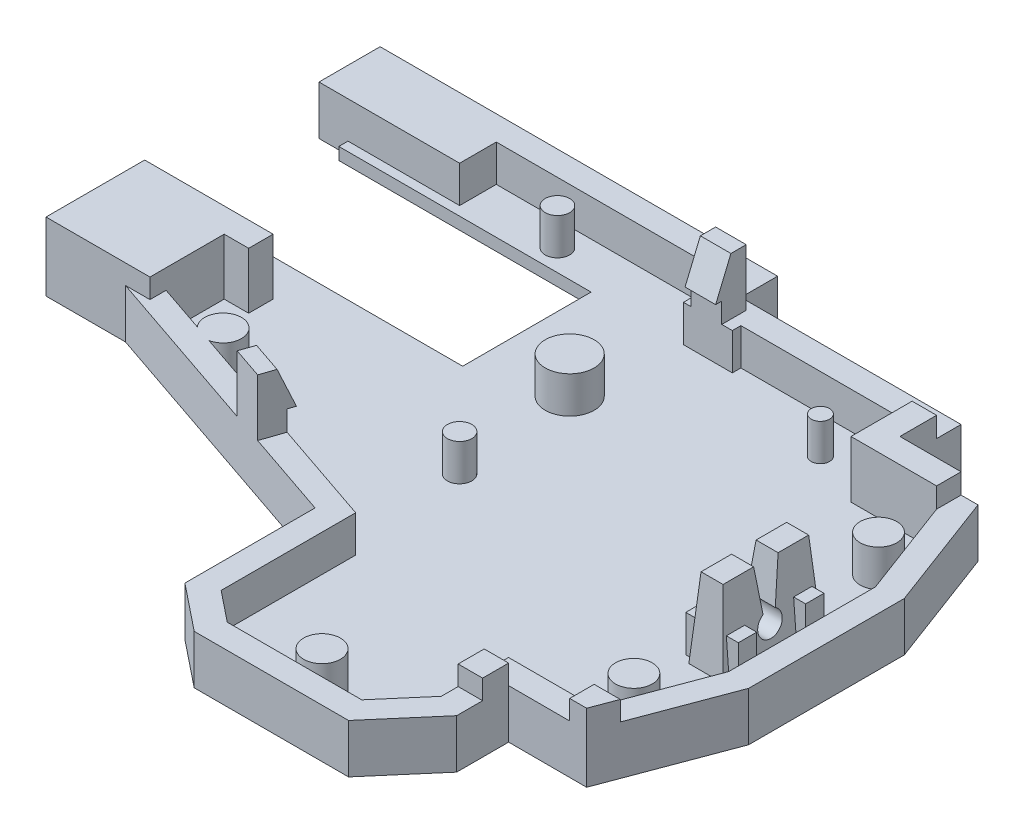
SolidWorks part; units mm, degrees
ref_plane "Front Plane" through (0, 0, 0) normal (0, 0, 1) x (1, 0, 0)
ref_plane "Top Plane" through (0, 0, 0) normal (0, 1, 0) x (1, 0, 0)
ref_plane "Right Plane" through (0, 0, 0) normal (1, 0, 0) x (0, 0, -1)
sketch "Sketch13" plane through (0, 0, 0) normal (0, 1, 0) x (1, 0, 0)
  line L1 (0, 0) -> (50, 0)
  line L2 (0, 0) -> (0, -45)
  line L3 (0, -45) -> (50, -45)
  line L4 (50, 0) -> (50, -45)
  dimension "D1" = 50
extrude "Boss-Extrude4" add sketch "Sketch13" along normal blind 1.6
sketch "Sketch14" plane through (0, 1.6, 0) normal (0, 1, 0) x (1, 0, 0)
  line L1 (50, 0) -> (40, 0)
  line L2 (50, 0) -> (50, -8)
  line L3 (50, -8) -> (40, -8)
  line L4 (40, 0) -> (40, -8)
extrude "Cut-Extrude6" cut sketch "Sketch14" against normal through all
sketch "Sketch15" plane through (0, 1.6, 0) normal (0, 1, 0) x (1, 0, 0)
  line L1 (40, 0) -> (22, 0)
  line L2 (40, 0) -> (40, -3)
  line L3 (40, -3) -> (22, -3)
  line L4 (22, 0) -> (22, -3)
extrude "Cut-Extrude7" cut sketch "Sketch15" against normal through all
sketch "Sketch16" plane through (0, 1.6, 0) normal (0, 1, 0) x (1, 0, 0)
  line L1 (22, -3) -> (26, -3)
  line L2 (22, -3) -> (22, -3.7)
  line L3 (22, -3.7) -> (26, -3.7)
  line L4 (26, -3) -> (26, -3.7)
  dimension "D1" = 0.7
  dimension "D2" = 4
extrude "Cut-Extrude8" cut sketch "Sketch16" against normal through all
sketch "Sketch17" plane through (0, 1.6, 0) normal (0, 1, 0) x (1, 0, 0)
  line L3 (40, -8) -> (50, -8) construction
  line L4 (47, -8) -> (50, -16)
  line L6 (50, -45) -> (50, -8) construction
  line L7 (50, -16) -> (65.8811, -16)
  line L8 (65.8811, -16) -> (65.8811, 17.9573)
  line L9 (65.8811, 17.9573) -> (47, 17.9573)
  line L10 (47, 17.9573) -> (47, -8)
extrude "Cut-Extrude9" cut sketch "Sketch17" against normal through all
sketch "Sketch18" plane through (0, 1.6, 0) normal (0, 1, 0) x (1, 0, 0)
  line L0 (40, -8) -> (40, -36) construction
  line L2 (40, -36) -> (61.1096, -36)
  line L3 (40, -36) -> (40, -58.8405)
  line L4 (40, -58.8405) -> (61.1096, -58.8405)
  line L5 (61.1096, -36) -> (61.1096, -58.8405)
extrude "Cut-Extrude10" cut sketch "Sketch18" against normal through all
sketch "Sketch21" plane through (0, 1.6, 0) normal (0, 1, 0) x (1, 0, 0)
  line L0 (50, -16) -> (27.9365, -16) construction
  line L1 (47, -36) -> (47, -28) construction
  line L2 (50, -36) -> (40, -36) construction
  line L3 (50, -28) -> (47, -36)
  line L4 (50, -36) -> (50, -16) construction
  line L5 (47, -36) -> (47, -49.2976)
  line L6 (47, -49.2976) -> (75.1968, -49.2976)
  line L7 (75.1968, -49.2976) -> (75.1968, -28)
  line L8 (75.1968, -28) -> (50, -28)
extrude "Cut-Extrude11" cut sketch "Sketch21" against normal through all
sketch "Sketch22" plane through (0, 1.6, 0) normal (0, 1, 0) x (1, 0, 0)
  line L0 (0, 0) -> (0, -19.3362) construction
  line L1 (0, 0) -> (0, -45) construction
  line L4 (0, -19.3362) -> (2, -19.3362)
  line L5 (0, -19.3362) -> (0, -22.3362)
  line L6 (0, -22.3362) -> (2, -22.3362)
  line L7 (2, -19.3362) -> (2, -22.3362)
  dimension "D1" = 2
  dimension "D2" = 3
extrude "Cut-Extrude12" cut sketch "Sketch22" against normal through all
sketch "Sketch23" plane through (0, 1.6, 0) normal (0, 1, 0) x (1, 0, 0)
  line L0 (40, -45) -> (23.5, -45) construction
  line L1 (0, -45) -> (40, -45) construction
  line L2 (23.5, -45) -> (23.5, -32)
  line L3 (0, -22.3362) -> (0, -26.3362) construction
  line L4 (0, -22.3362) -> (0, -45) construction
  line L5 (23.5, -32) -> (0, -26.3362)
  line L6 (0, -26.3362) -> (-30.2262, -26.3362)
  line L7 (-30.2262, -26.3362) -> (-30.2262, -63.1883)
  line L8 (-30.2262, -63.1883) -> (23.5, -63.1883)
  line L9 (23.5, -63.1883) -> (23.5, -45)
extrude "Cut-Extrude13" cut sketch "Sketch23" against normal through all
sketch "Sketch24" plane through (0, 1.6, 0) normal (0, 1, 0) x (1, 0, 0)
  line L0 (23.5, -43) -> (7.4911, -43)
  line L1 (23.5, -45) -> (40, -45) construction
  line L2 (7.4911, -43) -> (7.4911, -69.5502)
  line L3 (40, -36) -> (40, -45) construction
  line L4 (37, -45) -> (40, -41.5)
  line L5 (23.5, -45) -> (23.5, -32) construction
  line L6 (26, -45) -> (23.5, -43)
  line L7 (7.4911, -69.5502) -> (44.754, -69.5502)
  line L8 (44.754, -69.5502) -> (44.754, -41.5)
  line L9 (44.754, -41.5) -> (40, -41.5)
  line L10 (37, -45) -> (26, -45)
extrude "Cut-Extrude14" cut sketch "Sketch24" against normal through all
sketch "Sketch25" plane through (0, 1.6, 0) normal (0, 1, 0) x (1, 0, 0)
  line L0 (50, -22) -> (47.6007, -22.0598) construction
  line L1 (50, -28) -> (50, -16) construction
  line L2 (47.6007, -22.0598) -> (47.6007, -18.0598) construction
  line L4 (47.6007, -18.0598) -> (44.8007, -18.0598)
  line L5 (47.6007, -18.0598) -> (47.6007, -26.0598)
  line L6 (47.6007, -26.0598) -> (44.8007, -26.0598)
  line L7 (44.8007, -18.0598) -> (44.8007, -26.0598)
  dimension "D1" = 2.8
  dimension "D2" = 8
extrude "Cut-Extrude15" cut sketch "Sketch25" against normal through all
sketch "Sketch28" plane through (0, 0, 0) normal (0, -1, 0) x (1, 0, 0)
  line L44 (42, 38) -> (42, 42.2398)
  line L45 (42, 42.2398) -> (37.9199, 47)
  line L46 (37.9199, 47) -> (25.2984, 47)
  line L47 (25.2984, 47) -> (21.5, 43.9612)
  line L48 (21.5, 43.9612) -> (21.5, 33.5752)
  line L49 (21.5, 33.5752) -> (-2, 27.9115)
  line L50 (-2, 27.9115) -> (-2, -2)
  line L51 (-2, -2) -> (24, -2)
  line L52 (24, -2) -> (24, 1)
  line L53 (24, 1) -> (42, 1)
  line L54 (42, 1) -> (42, 6)
  line L55 (42, 6) -> (48.386, 6)
  line L56 (48.386, 6) -> (52, 15.6373)
  line L57 (52, 15.6373) -> (52, 28.3627)
  line L58 (52, 28.3627) -> (48.386, 38)
  line L59 (48.386, 38) -> (42, 38)
  line L60 (42, 38) -> (42, 42.2398)
  line L61 (42, 42.2398) -> (37.9199, 47)
  line L62 (37.9199, 47) -> (25.2984, 47)
  line L63 (25.2984, 47) -> (21.5, 43.9612)
  line L64 (21.5, 43.9612) -> (21.5, 33.5752)
  line L65 (21.5, 33.5752) -> (-2, 27.9115)
  line L66 (-2, 27.9115) -> (-2, -2)
  line L67 (-2, -2) -> (24, -2)
  line L68 (24, -2) -> (24, 1)
  line L69 (24, 1) -> (42, 1)
  line L70 (42, 1) -> (42, 6)
  line L71 (42, 6) -> (48.386, 6)
  line L72 (48.386, 6) -> (52, 15.6373)
  line L73 (52, 15.6373) -> (52, 28.3627)
  line L74 (52, 28.3627) -> (48.386, 38)
  line L75 (48.386, 38) -> (42, 38)
  dimension "D1" = 2
extrude "Boss-Extrude6" add sketch "Sketch28" along normal blind 6
sketch "Sketch30" plane through (0, 0, 0) normal (0, 1, 0) x (1, 0, 0)
  line L8 (44.8007, -18.0598) -> (44.8007, -26.0598)
  line L9 (44.8007, -26.0598) -> (47.6007, -26.0598)
  line L10 (47.6007, -26.0598) -> (47.6007, -18.0598)
  line L11 (47.6007, -18.0598) -> (44.8007, -18.0598)
  line L12 (44.8007, -18.0598) -> (44.8007, -26.0598)
  line L13 (44.8007, -26.0598) -> (47.6007, -26.0598)
  line L14 (47.6007, -26.0598) -> (47.6007, -18.0598)
  line L15 (47.6007, -18.0598) -> (44.8007, -18.0598)
  dimension "D1" = 0
extrude "Boss-Extrude7" add sketch "Sketch30" along normal blind 3.5
sketch "Sketch31" plane through (0, 1.6, 0) normal (0, 1, 0) x (1, 0, 0)
  line L44 (37, -45) -> (40, -41.5)
  line L45 (40, -41.5) -> (40, -36)
  line L46 (40, -36) -> (47, -36)
  line L47 (47, -36) -> (50, -28)
  line L48 (50, -28) -> (50, -16)
  line L49 (50, -16) -> (47, -8)
  line L50 (47, -8) -> (40, -8)
  line L51 (40, -8) -> (40, -3)
  line L52 (40, -3) -> (26, -3)
  line L53 (26, -3) -> (26, -3.7)
  line L54 (26, -3.7) -> (22, -3.7)
  line L55 (22, -3.7) -> (22, 0)
  line L56 (22, 0) -> (0, 0)
  line L57 (0, 0) -> (0, -19.3362)
  line L58 (0, -19.3362) -> (2, -19.3362)
  line L59 (2, -19.3362) -> (2, -22.3362)
  line L60 (2, -22.3362) -> (0, -22.3362)
  line L61 (0, -22.3362) -> (0, -26.3362)
  line L62 (0, -26.3362) -> (23.5, -32)
  line L63 (23.5, -32) -> (23.5, -43)
  line L64 (23.5, -43) -> (26, -45)
  line L65 (26, -45) -> (37, -45)
  line L66 (37, -45) -> (40, -41.5)
  line L67 (40, -41.5) -> (40, -36)
  line L68 (40, -36) -> (47, -36)
  line L69 (47, -36) -> (50, -28)
  line L70 (50, -28) -> (50, -16)
  line L71 (50, -16) -> (47, -8)
  line L72 (47, -8) -> (40, -8)
  line L73 (40, -8) -> (40, -3)
  line L74 (40, -3) -> (26, -3)
  line L75 (26, -3) -> (26, -3.7)
  line L76 (26, -3.7) -> (22, -3.7)
  line L77 (22, -3.7) -> (22, 0)
  line L78 (22, 0) -> (0, 0)
  line L79 (0, 0) -> (0, -19.3362)
  line L80 (0, -19.3362) -> (2, -19.3362)
  line L81 (2, -19.3362) -> (2, -22.3362)
  line L82 (2, -22.3362) -> (0, -22.3362)
  line L83 (0, -22.3362) -> (0, -26.3362)
  line L84 (0, -26.3362) -> (23.5, -32)
  line L85 (23.5, -32) -> (23.5, -43)
  line L86 (23.5, -43) -> (26, -45)
  line L87 (26, -45) -> (37, -45)
  dimension "D1" = 0
extrude "Cut-Extrude16" cut sketch "Sketch31" against normal blind 4.6
sketch "Sketch32" plane through (0, 1.6, 0) normal (0, -1, 0) x (1, 0, 0)
  line L8 (47.6007, 18.0598) -> (47.6007, 26.0598)
  line L9 (47.6007, 26.0598) -> (44.8007, 26.0598)
  line L10 (44.8007, 26.0598) -> (44.8007, 18.0598)
  line L11 (44.8007, 18.0598) -> (47.6007, 18.0598)
  line L12 (47.6007, 18.0598) -> (47.6007, 26.0598)
  line L13 (47.6007, 26.0598) -> (44.8007, 26.0598)
  line L14 (44.8007, 26.0598) -> (44.8007, 18.0598)
  line L15 (44.8007, 18.0598) -> (47.6007, 18.0598)
  dimension "D1" = 0
extrude "Boss-Extrude8" add sketch "Sketch32" along normal blind 4.6
sketch "Sketch35" plane through (47.6007, 0, 0) normal (1, 0, 0) x (0, 0, -1)
  line L0 (-22.0598, 3.5) -> (-22.0598, 0) construction
  line L1 (-26.0598, 3.5) -> (-18.0598, 3.5) construction
  line L2 (-22.0598, 3.5) -> (-21.0598, 3.5) construction
  line L3 (-22.0598, 3.5) -> (-23.0598, 3.5) construction
  line L4 (-22.0598, 0) -> (-21.5598, 0)
  line L5 (-21.5598, 0) -> (-21.0598, 3.5)
  line L6 (-22.0598, 0) -> (-22.5598, 0)
  line L7 (-22.5598, 0) -> (-23.0598, 3.5)
  line L8 (-23.0598, 3.5) -> (-23.2577, 4.8851)
  line L9 (-21.0598, 3.5) -> (-21.2977, 5.1651)
  line L10 (-21.2977, 5.1651) -> (-23.2577, 4.8851)
extrude "Cut-Extrude18" cut sketch "Sketch35" against normal blind 4.6
sketch "Sketch37" plane through (47.6007, 0, 0) normal (1, 0, 0) x (0, 0, -1)
  line L0 (-22.0598, 0) -> (-22.0598, -3.4808) construction
  line L1 (-22.5598, 0) -> (-21.5598, 0) construction
  line L2 (-21.5598, 0) -> (-22.0598, -0.866) construction
  circle A0 centre (-22.0598, -0.866) radius 1
extrude "Cut-Extrude19" cut sketch "Sketch37" against normal blind 4.6
sketch "Sketch39" plane through (44.8007, 0, 0) normal (-1, 0, 0) x (0, 0, 1)
  line L0 (26.0598, 3.5) -> (25.5598, 3.5) construction
  line L1 (23.0598, 3.5) -> (26.0598, 3.5) construction
  line L2 (25.5598, 3.5) -> (26.0598, -3)
  line L3 (26.0598, -3) -> (27.9064, -2.858)
  line L4 (27.9064, -2.858) -> (27.4064, 3.642)
  line L5 (27.4064, 3.642) -> (25.5598, 3.5)
  line L6 (18.0598, 3.5) -> (18.5598, 3.5) construction
  line L7 (18.0598, 3.5) -> (21.0598, 3.5) construction
  line L8 (18.5598, 3.5) -> (18.0598, -3)
  line L9 (18.0598, -3) -> (15.9573, -2.8383)
  line L10 (15.9573, -2.8383) -> (16.4557, 3.642)
  line L11 (16.4557, 3.642) -> (18.5598, 3.5)
extrude "Cut-Extrude20" cut sketch "Sketch39" against normal blind 4.6
sketch "Sketch41" plane through (0, 0, 0) normal (0, 0, 1) x (1, 0, 0)
  line L0 (44.8007, 3.5) -> (45.3007, 3.5) construction
  line L1 (44.8007, 3.5) -> (47.6007, 3.5) construction
  line L2 (47.6007, 3.5) -> (47.1007, 3.5) construction
  line L3 (45.3007, 3.5) -> (44.8007, -3)
  line L4 (44.8007, -3) -> (43.415, -2.8934)
  line L5 (43.415, -2.8934) -> (43.9406, 3.9398)
  line L6 (43.9406, 3.9398) -> (45.3007, 3.5)
  line L7 (47.1007, 3.5) -> (47.6007, -3)
  line L8 (47.6007, -3) -> (49.659, -2.8417)
  line L9 (49.659, -2.8417) -> (49.1373, 3.9398)
  line L10 (49.1373, 3.9398) -> (47.1007, 3.5)
extrude "Cut-Extrude21" cut sketch "Sketch41" along normal up to vertex
sketch "Sketch43" plane through (0, 0, 0) normal (0, 1, 0) x (1, 0, 0)
  line L0 (47, -8) -> (50, -16)
  line L1 (50, -16) -> (51.1704, -13.4251)
  line L2 (49.4404, -8.8117) -> (52, -15.6373) construction
  line L3 (46.2007, -6) -> (51.8278, -6) construction
  line L4 (45.0315, -6) -> (47.37, -6) construction
  line L5 (50.6159, -11.9464) -> (47.8466, -4.5615) construction
  line L6 (51.1704, -13.4251) -> (48.386, -6)
  line L7 (48.386, -6) -> (42.8188, -6)
  line L8 (42, -6) -> (43.6375, -6) construction
  line L9 (42.8188, -6) -> (42.8188, -8)
  line L10 (40, -8) -> (43.6375, -8) construction
  line L11 (42.8188, -8) -> (47, -8)
extrude "Boss-Extrude9" add sketch "Sketch43" against normal blind 4.6
sketch "Sketch44" plane through (0, -3, 0) normal (0, 1, 0) x (1, 0, 0)
  line L0 (47.6007, -18.0598) -> (47.6007, -18.5598) construction
  line L1 (47.6007, -18.0598) -> (47.6007, -26.0598) construction
  line L2 (47.6007, -18.5598) -> (48.3507, -18.5598) construction
  line L3 (44.8007, -18.5598) -> (44.0507, -18.5598) construction
  line L4 (44.8007, -26.0598) -> (44.8007, -18.0598) construction
  line L5 (47.6007, -26.0598) -> (47.6007, -25.5598) construction
  line L6 (48.3507, -25.5598) -> (44.0507, -25.5598) construction
  line L7 (48.3507, -18.5598) -> (48.3507, -20.0598)
  line L8 (48.3507, -25.5598) -> (48.3507, -24.0598)
  line L9 (48.3507, -24.0598) -> (44.0507, -24.0598)
  line L10 (44.0507, -24.0598) -> (44.0507, -25.5598)
  line L11 (44.0507, -25.5598) -> (48.3507, -25.5598)
  line L12 (48.3507, -20.0598) -> (44.0507, -20.0598)
  line L13 (44.0507, -20.0598) -> (44.0507, -18.5598)
  line L14 (44.0507, -18.5598) -> (48.3507, -18.5598)
extrude "Boss-Extrude11" add sketch "Sketch44" along normal blind 3
sketch "Sketch45" plane through (0, -3, 0) normal (0, 1, 0) x (1, 0, 0)
  line L0 (50, -22) -> (44, -22) construction
  line L1 (50, -28) -> (50, -16) construction
  line L2 (44, -22) -> (44, -32) construction
  line L3 (44, -32) -> (46.25, -32) construction
  line L4 (44, -22) -> (44, -12) construction
  line L5 (22, -3.7) -> (22, -22) construction
  line L6 (22, -22) -> (22, -21) construction
  line L7 (40, -36) -> (23.5, -36) construction
  line L8 (23.5, -32) -> (23.5, -43) construction
  line L9 (31.75, -45) -> (31.75, -43) construction
  line L10 (26, -45) -> (37, -45) construction
  line L11 (40, -3) -> (40, -6) construction
  line L12 (40, -8) -> (40, -3) construction
  line L13 (40, -6) -> (35.5, -6) construction
  line L14 (22, 0) -> (22, -2) construction
  line L15 (22, 0) -> (0, 0) construction
  line L16 (22, -3.7) -> (22, 0) construction
  line L17 (22, -2) -> (10, -2) construction
  line L18 (0, -24.3362) -> (5, -24.3362) construction
  line L19 (0, -22.3362) -> (0, -26.3362) construction
  circle A0 centre (46.25, -12) radius 1.5
  circle A1 centre (46.25, -32) radius 1.5
  circle A2 centre (22, -22) radius 1
  circle A3 centre (21, -12) radius 1.9996
  circle A4 centre (31.75, -43) radius 1.5033
  circle A5 centre (35.5, -6) radius 0.75
  circle A6 centre (10, -2) radius 1
  circle A7 centre (5, -24.3362) radius 1.5
extrude "Boss-Extrude12" add sketch "Sketch45" along normal blind 3
sketch "Sketch46" plane through (0, 0, 0) normal (0, 1, 0) x (1, 0, 0)
  line L0 (14.1373, -29.7435) -> (16.5677, -30.3292)
  line L1 (16.5677, -30.3292) -> (16.0991, -32.2736)
  line L2 (21.5, -33.5752) -> (-2, -27.9115) construction
  line L3 (16.0991, -32.2736) -> (13.6687, -31.6878)
  line L4 (13.6687, -31.6878) -> (14.1373, -29.7435)
  line L5 (24, -3.7) -> (25.1336, -3.7) construction
  line L6 (22, -3.7) -> (26, -3.7) construction
  line L7 (25.1336, -3.7) -> (22.6336, -3.7)
  line L8 (22.6336, -3.7) -> (22.6336, -1.7)
  line L9 (22.6336, -1.7) -> (25.1336, -1.7)
  line L10 (25.1336, -1.7) -> (25.1336, -3.7)
  line L11 (2, -20.8362) -> (2, -19.9327) construction
  line L12 (2, -22.3362) -> (2, -19.3362) construction
  line L13 (2, -19.9327) -> (2, -21.9327)
  line L14 (2, -21.9327) -> (0, -21.9327)
  line L15 (0, -21.9327) -> (0, -19.9327)
  line L16 (0, -19.9327) -> (2, -19.9327)
  line L17 (23.5, -32) -> (0, -26.3362) construction
  line L18 (16.5677, -30.3292) -> (14.1373, -29.7435) construction
  line L19 (47, -36) -> (48.8727, -36.7022)
  line L20 (52, -28.3627) -> (48.386, -38) construction
  line L21 (48.8727, -36.7022) -> (49.7505, -34.3614)
  line L22 (49.7505, -34.3614) -> (47.8778, -33.6592)
  line L23 (50, -28) -> (47, -36) construction
  line L24 (47.8778, -33.6592) -> (47, -36)
  line L25 (40, -3) -> (40, -8)
  line L26 (26, -3) -> (40, -3) construction
  line L27 (40, -3) -> (40, -8) construction
  line L28 (40, -8) -> (47, -8)
  line L29 (47, -8) -> (47, -6)
  line L30 (42, -6) -> (48.386, -6) construction
  line L31 (47, -6) -> (42, -6)
  line L32 (42, -6) -> (42, -3)
  line L33 (42, -1) -> (42, -6) construction
  line L34 (42, -3) -> (40, -3)
extrude "Boss-Extrude13" add sketch "Sketch46" along normal blind 1.65
sketch "Sketch47" plane through (0, 0, 0) normal (0, 1, 0) x (1, 0, 0)
  line L1 (0, 0) -> (3, 0)
  line L2 (0, 0) -> (0, -3)
  line L3 (0, -3) -> (3, -3)
  line L4 (3, 0) -> (3, -3)
extrude "Boss-Extrude14" add sketch "Sketch47" against normal up to surface (3 mm away) up to face at (10, -3, 3)
sketch "Sketch48" plane through (0, 0, 0) normal (0, 1, 0) x (1, 0, 0)
  line L0 (-2, -27.9115) -> (-2, 2) construction
  line L1 (0, -19.3362) -> (-2, -19.3362)
  line L2 (0, -19.3362) -> (0, -3)
  line L3 (0, -3) -> (-2, -3)
  line L4 (-2, -19.3362) -> (-2, -3)
extrude "Cut-Extrude22" cut sketch "Sketch48" against normal up to surface (3 mm away) up to face at (23.75, -3, 19.4826)
sketch "Sketch49" plane through (-2, 0, 0) normal (-1, 0, 0) x (0, 0, 1)
  line L1 (-2, -6) -> (19.3362, -6)
  line L2 (-2, -6) -> (-2, -3)
  line L3 (-2, -3) -> (19.3362, -3)
  line L4 (19.3362, -6) -> (19.3362, -3)
extrude "Boss-Extrude15" add sketch "Sketch49" along normal blind 13
sketch "Sketch50" plane through (0, -6, 0) normal (0, -1, 0) x (1, 0, 0)
  line L0 (52, 22) -> (52, -11.4177) construction
  line L1 (52, 15.6373) -> (52, 28.3627) construction
  line L2 (24, -2) -> (52, -2) construction
  line L3 (52, 22) -> (52, 58.8348) construction
  line L4 (34.4271, 47) -> (52, 47) construction
  line L5 (37.9199, 47) -> (25.2984, 47) construction
  line L7 (-15, -2) -> (52, -2)
  line L8 (-15, -2) -> (-15, 47)
  line L9 (-15, 47) -> (52, 47)
  line L10 (52, -2) -> (52, 47)
extrude "Boss-Extrude16" add sketch "Sketch50" against normal up to surface (3 mm away) up to face at (19.6296, -3, 17.9784)
sketch "Sketch51" plane through (0, -3, 0) normal (0, 1, 0) x (1, 0, 0)
  line L0 (47.6007, -26.0598) -> (47.6007, -47) construction
  line L1 (52, -47) -> (37.9199, -47) construction
  line L3 (47, -36) -> (52, -36)
  line L4 (47, -36) -> (47, -47)
  line L5 (47, -47) -> (52, -47)
  line L6 (52, -36) -> (52, -47)
extrude "Boss-Extrude17" add sketch "Sketch51" along normal blind 15.6
sketch "Sketch52" plane through (0, 1.65, 0) normal (0, 1, 0) x (1, 0, 0)
  line L8 (47.8778, -33.6592) -> (47, -36)
  line L9 (47, -36) -> (49.136, -36)
  line L10 (49.136, -36) -> (49.7505, -34.3614)
  line L11 (49.7505, -34.3614) -> (47.8778, -33.6592)
  line L12 (47.8778, -33.6592) -> (47, -36)
  line L13 (47, -36) -> (49.136, -36)
  line L14 (49.136, -36) -> (49.7505, -34.3614)
  line L15 (49.7505, -34.3614) -> (47.8778, -33.6592)
  dimension "D1" = 0
extrude "Cut-Extrude23" cut sketch "Sketch52" against normal up to surface (1.65 mm away) up to face at (49.3349, 0, 19.5578)
sketch "Sketch53" plane through (0, 0, 0) normal (0, 1, 0) x (1, 0, 0)
  line L0 (40, -36) -> (40, -41.5) construction
  line L1 (40, -37.9906) -> (42, -37.9906)
  line L2 (40, -37.9906) -> (40, -40.1199)
  line L3 (40, -40.1199) -> (42, -40.1199)
  line L4 (42, -37.9906) -> (42, -40.1199)
  line L5 (42, -38) -> (42, -42.2398) construction
extrude "Boss-Extrude18" add sketch "Sketch53" along normal blind 1.6
sketch "Sketch55" plane through (0, 1.65, 0) normal (0, 1, 0) x (1, 0, 0)
  line L1 (22.6336, -1.7) -> (25.1336, -1.7)
  line L2 (22.6336, -1.7) -> (22.6336, -4.2)
  line L3 (22.6336, -4.2) -> (25.1336, -4.2)
  line L4 (25.1336, -1.7) -> (25.1336, -4.2)
extrude "Boss-Extrude20" add sketch "Sketch55" along normal blind 3
sketch "Sketch56" plane through (25.1336, 0, 0) normal (1, 0, 0) x (0, 0, -1)
  line L0 (-4.2, 1.65) -> (-2.95, 4.65)
  line L1 (-4.2, 4.65) -> (-1.7, 4.65) construction
  line L2 (-2.95, 4.65) -> (-2.95, 7.6873)
  line L3 (-2.95, 7.6873) -> (-6.5972, 7.6873)
  line L4 (-6.5972, 7.6873) -> (-6.5972, 1.6413)
  line L5 (-6.5972, 1.6413) -> (-4.2, 1.65)
extrude "Cut-Extrude24" cut sketch "Sketch56" against normal blind 3
sketch "Sketch58" plane through (0, -3, 0) normal (0, 1, 0) x (1, 0, 0)
  line L0 (3, 0) -> (-15, 0) construction
  line L1 (-15, -47) -> (-15, 2) construction
  line L2 (0, -26.3362) -> (7.3396, -26.3362) construction
  line L3 (-15, -19.3362) -> (-15, -16.4918) construction
  line L4 (3, 0) -> (3, -3.75) construction
  line L5 (3, -3.75) -> (-5.5, -3.75) construction
  line L6 (-5.5, -3.75) -> (14.5, -3.75)
  line L7 (-5.5, -3.75) -> (-5.5, -14.25)
  line L8 (-5.5, -14.25) -> (14.5, -14.25)
  line L9 (14.5, -3.75) -> (14.5, -14.25)
  line L10 (7.3396, 0) -> (7.3396, -26.3362) construction
  line L11 (22, 0) -> (3, 0) construction
  line L12 (26, -45) -> (6.087, -45) construction
  line L13 (6.087, 0) -> (6.087, -45) construction
  line L14 (0, 0) -> (0, -25) construction
  line L15 (0, -22.3362) -> (0, -26.3362) construction
  line L16 (0, -14.25) -> (0, -17.2489) construction
  line L17 (2, -20.8362) -> (2, -17.2489) construction
  line L18 (2, -19.3362) -> (2, -22.3362) construction
  line L19 (0, -17.2489) -> (2, -17.2489)
  line L20 (2, -17.2489) -> (2, -19.2489)
  line L21 (2, -19.2489) -> (0, -19.2489)
  line L22 (0, -19.2489) -> (0, -17.2489)
extrude "Cut-Extrude29" cut sketch "Sketch58" against normal blind 1
sketch "Sketch60" plane through (0, -3, 0) normal (0, 1, 0) x (1, 0, 0)
  line L0 (27.9182, -45) -> (13.2629, -45) construction
  line L1 (26, -45) -> (37, -45) construction
  line L2 (23.5, -32) -> (23.5, -45) construction
  line L3 (0, 0) -> (0, -24) construction
  line L4 (0, -22.3362) -> (0, -26.3362) construction
  line L5 (0, -24) -> (23.5, -32)
  line L6 (23.5, -32) -> (0, -26.3362)
  line L7 (0, -26.3362) -> (23.5, -32) construction
  line L8 (0, -26.3362) -> (0, -24)
extrude "Boss-Extrude21" add sketch "Sketch60" along normal up to surface (3 mm away) up to face at (49.1691, 0, 20)
sketch "Sketch61" plane through (-5.9989, 0, 24.8904) normal (0.2343, 0, -0.9722) x (-0.9722, 0, -0.2343)
  line L8 (-23.2128, 1.65) -> (-23.2128, 0)
  line L9 (-23.2128, 0) -> (-20.7128, 0)
  line L10 (-20.7128, 0) -> (-20.7128, 1.65)
  line L11 (-20.7128, 1.65) -> (-23.2128, 1.65)
  line L12 (-23.2128, 1.65) -> (-23.2128, 0)
  line L13 (-23.2128, 0) -> (-20.7128, 0)
  line L14 (-20.7128, 0) -> (-20.7128, 1.65)
  line L15 (-20.7128, 1.65) -> (-23.2128, 1.65)
  dimension "D1" = 0
extrude "Boss-Extrude22" add sketch "Sketch61" along normal up to surface (0.8848 mm away)
sketch "Sketch62" plane through (0, 0, 0) normal (0, 1, 0) x (1, 0, 0)
  line L0 (0, -24) -> (0, -26) construction
  line L1 (1.9318, -24.6576) -> (-9.2599, -20.8477) construction
  line L2 (3.8635, -25.3152) -> (0, -24) construction
  line L3 (-9.2599, -20.8477) -> (-9.2599, -22.8477) construction
  line L4 (0, -26) -> (-0.5452, -28.2621)
  line L5 (13.6687, -31.6878) -> (-2, -27.9115) construction
  line L6 (-0.5452, -28.2621) -> (-9.9311, -26)
  line L7 (-9.9311, -26) -> (-9.2599, -22.8477)
  line L8 (-9.2599, -22.8477) -> (0, -26)
extrude "Cut-Extrude30" cut sketch "Sketch62" against normal up to surface (3 mm away) up to face at (35.5, -3, 6.75)
sketch "Sketch63" plane through (-6.4675, 0, 26.8348) normal (-0.2343, 0, 0.9722) x (0.9722, 0, 0.2343)
  line L16 (20.7128, 0) -> (6.0919, 0)
  line L17 (6.0919, 0) -> (6.0919, -3)
  line L18 (6.0919, -3) -> (28.7683, -3)
  line L19 (28.7683, -3) -> (28.7683, 0)
  line L20 (28.7683, 0) -> (23.2128, 0)
  line L21 (23.2128, 0) -> (23.2128, 1.65)
  line L22 (23.2128, 1.65) -> (20.7128, 1.65)
  line L23 (20.7128, 1.65) -> (20.7128, 0)
  line L24 (20.7128, 0) -> (6.0919, 0)
  line L25 (6.0919, 0) -> (6.0919, -3)
  line L26 (6.0919, -3) -> (28.7683, -3)
  line L27 (28.7683, -3) -> (28.7683, 0)
  line L28 (28.7683, 0) -> (23.2128, 0)
  line L29 (23.2128, 0) -> (23.2128, 1.65)
  line L30 (23.2128, 1.65) -> (20.7128, 1.65)
  line L31 (20.7128, 1.65) -> (20.7128, 0)
  dimension "D1" = 0
extrude "Cut-Extrude31" cut sketch "Sketch63" against normal up to surface (0.7539 mm away)
sketch "Sketch64" plane through (0, 1.65, 0) normal (0, 1, 0) x (1, 0, 0)
  line L0 (0, -21.9327) -> (0, -22.9624) construction
  line L2 (0, -22.9624) -> (2.5515, -22.9624)
  line L3 (0, -22.9624) -> (0, -18.6516)
  line L4 (0, -18.6516) -> (2.5515, -18.6516)
  line L5 (2.5515, -22.9624) -> (2.5515, -18.6516)
extrude "Cut-Extrude32" cut sketch "Sketch64" against normal up to surface (4.65 mm away) up to face at (18.4683, -3, 21.8358)
sketch "Sketch65" plane through (0, -4, 0) normal (0, 1, 0) x (1, 0, 0)
  line L8 (0, -17.2489) -> (0, -19.2489)
  line L9 (0, -19.2489) -> (2, -19.2489)
  line L10 (2, -19.2489) -> (2, -17.2489)
  line L11 (2, -17.2489) -> (0, -17.2489)
  line L12 (0, -17.2489) -> (0, -19.2489)
  line L13 (0, -19.2489) -> (2, -19.2489)
  line L14 (2, -19.2489) -> (2, -17.2489)
  line L15 (2, -17.2489) -> (0, -17.2489)
  dimension "D1" = 0
extrude "Boss-Extrude23" add sketch "Sketch65" along normal up to surface (4 mm away) up to face at (49.1691, 0, 20)
sketch "Sketch66" plane through (0, 0, 0) normal (0, 1, 0) x (1, 0, 0)
  line L1 (0, -19.2489) -> (2, -19.2489)
  line L2 (0, -19.2489) -> (0, -17.2489)
  line L3 (0, -17.2489) -> (2, -17.2489)
  line L4 (2, -19.2489) -> (2, -17.2489)
extrude "Boss-Extrude24" add sketch "Sketch66" along normal blind 1.6
sketch "Sketch67" plane through (0, 1.6, 0) normal (0, 1, 0) x (1, 0, 0)
  line L0 (0, -19.2489) -> (2.5, -19.2489)
  line L1 (0, -19.2489) -> (0, -17.2489)
  line L2 (0, -17.2489) -> (2.5, -17.2489)
  line L3 (2.5, -17.2489) -> (2.5, -19.2489)
extrude "Boss-Extrude25" add sketch "Sketch67" along normal blind 3
sketch "Sketch68" plane through (0, 0, 17.2489) normal (0, 0, -1) x (-1, 0, 0)
  line L0 (-2.5, 1.6) -> (-1.25, 4.6)
  line L1 (-2.5, 4.6) -> (0, 4.6) construction
  line L2 (-1.25, 4.6) -> (-1.25, 6.7749)
  line L3 (-1.25, 6.7749) -> (-4.4975, 6.7749)
  line L4 (-4.4975, 6.7749) -> (-4.4975, 1.5671)
  line L5 (-4.4975, 1.5671) -> (-2.5, 1.6)
extrude "Cut-Extrude33" cut sketch "Sketch68" against normal blind 3
sketch "Sketch69" plane through (0, 1.65, 0) normal (0, 1, 0) x (1, 0, 0)
  line L0 (14.3446, -28.8833) -> (16.7212, -29.6923) construction
  line L1 (16.7212, -29.6923) -> (18.8289, -30.4098) construction
  line L2 (16.2758, -31.5407) -> (16.8859, -29.7484) construction
  line L3 (16.2758, -31.5407) -> (16.7212, -29.6923) construction
  line L4 (16.2758, -31.5407) -> (13.8992, -30.7316) construction
  line L5 (14.3446, -28.8833) -> (16.8859, -29.7484)
  line L6 (16.8859, -29.7484) -> (16.2758, -31.5407)
  line L7 (16.2758, -31.5407) -> (12.9279, -30.401) construction
  line L8 (14.3446, -28.8833) -> (13.7345, -30.6756)
  line L9 (13.7345, -30.6756) -> (16.2758, -31.5407)
extrude "Boss-Extrude26" add sketch "Sketch69" against normal up to surface (1.65 mm away) up to face at (49.1691, 0, 20)
sketch "Sketch70" plane through (0, 0, 19.2489) normal (0, 0, 1) x (1, 0, 0)
  line L0 (2.5, 1.6) -> (1.25, 4.6) construction
  line L1 (2.5, 1.6) -> (-2.555, 1.6)
  line L2 (2.5, 1.6) -> (2.5, 7.1604)
  line L3 (2.5, 7.1604) -> (-2.555, 7.1604)
  line L4 (-2.555, 1.6) -> (-2.555, 7.1604)
extrude "Cut-Extrude34" cut sketch "Sketch70" against normal blind 3
sketch "Sketch71" plane through (0, 1.65, 0) normal (0, 1, 0) x (1, 0, 0)
  line L0 (16.2758, -31.5407) -> (17.0814, -29.1741)
  line L1 (16.2758, -31.5407) -> (13.7345, -30.6756)
  line L2 (18.2187, -25.945) -> (17.0814, -29.1741) construction
  line L3 (18.2187, -25.945) -> (16.2758, -31.5407) construction
  line L4 (17.0814, -29.1741) -> (11.4228, -27.2093) construction
  line L5 (13.7345, -30.6756) -> (14.5598, -28.2985)
  line L6 (14.5598, -28.2985) -> (17.0814, -29.1741)
extrude "Boss-Extrude27" add sketch "Sketch71" along normal blind 3
sketch "Sketch72" plane through (24.2076, 0, 8.2409) normal (0.9466, 0, 0.3223) x (0.3223, 0, -0.9466)
  line L0 (-22.1129, 1.65) -> (-23.3629, 4.65)
  line L1 (-24.6129, 4.65) -> (-22.1129, 4.65) construction
  line L2 (-23.3629, 4.65) -> (-23.3629, 7.6948)
  line L3 (-23.3629, 7.6948) -> (-20.7348, 7.6948)
  line L4 (-20.7348, 7.6948) -> (-20.7348, 1.65)
  line L5 (-20.7348, 1.65) -> (-22.1129, 1.65)
extrude "Cut-Extrude35" cut sketch "Sketch72" against normal blind 3
sketch "Sketch73" plane through (21.762, 0, 7.5561) normal (-0.9447, 0, -0.328) x (-0.328, 0, 0.9447)
  line L10 (24.4734, 4.65) -> (23.2234, 4.65)
  line L11 (23.2234, 4.65) -> (21.9734, 1.65)
  line L12 (21.9734, 1.65) -> (22.5801, 1.65)
  line L13 (22.5801, 1.65) -> (24.4734, 1.65)
  line L14 (24.4734, 1.65) -> (24.4734, 4.65)
  line L15 (24.4734, 4.65) -> (23.2234, 4.65)
  line L16 (23.2234, 4.65) -> (21.9734, 1.65)
  line L17 (21.9734, 1.65) -> (22.5801, 1.65)
  line L18 (22.5801, 1.65) -> (24.4734, 1.65)
  line L19 (24.4734, 1.65) -> (24.4734, 4.65)
  dimension "D1" = 0
extrude "Boss-Extrude28" add sketch "Sketch73" along normal up to surface (0.0115 mm away)
sketch "Sketch74" plane through (0, -4, 0) normal (0, 1, 0) x (1, 0, 0)
  line L0 (-5.5, -9) -> (14.5, -9) construction
  line L1 (-5.5, -3.75) -> (-5.5, -14.25) construction
  line L2 (14.5, -14.25) -> (14.5, -3.75) construction
  line L3 (-0.25, -6.1692) -> (-0.25, -11.6692) construction
  line L4 (4.5, -6.1692) -> (4.5, -11.6692) construction
  line L5 (-0.25, -6.1692) -> (9.25, -6.1692) construction
  line L6 (9.25, -6.1692) -> (9.25, -11.6692) construction
  line L7 (2.5808, -9) -> (-0.25, -6.1692) construction
  line L8 (6.4192, -6.1692) -> (2.5808, -6.1692)
  line L9 (9.25, -6.1692) -> (6.4192, -9) construction
  line L10 (6.4192, -11.8308) -> (2.5808, -11.8308)
  arc A0 (2.5808, -6.1692) -> (2.5808, -11.8308) centre (2.5808, -9) ccw
  arc A1 (6.4192, -6.1692) -> (6.4192, -11.8308) centre (6.4192, -9) cw
extrude "Cut-Extrude36" cut sketch "Sketch74" against normal blind 3
fillet "Fillet8" radius 1 4 edges at (-0.25, -6, 9) (4.5, -6, 6.1692) (9.25, -6, 9) (4.5, -6, 11.8308)
sketch "Sketch76" plane through (0, -3, 0) normal (0, 1, 0) x (1, 0, 0)
  line L0 (47, -47) -> (-8, -47) construction
  line L1 (25.2984, -47) -> (-15, -47) construction
  line L2 (-15, -47) -> (-15, -32.5)
  line L3 (-15, -47) -> (-15, 2) construction
  line L4 (-15, -32.5) -> (-8, -32.5)
  line L5 (-8, -32.5) -> (-8, -47)
  line L6 (-8, -47) -> (-15, -47)
extrude "Boss-Extrude29" add sketch "Sketch76" along normal blind 14.5
sketch "Sketch79" plane through (21.6663, 0, 7.3758) normal (-0.9466, 0, -0.3223) x (-0.3223, 0, 0.9466)
  line L12 (22.7196, 0) -> (24.6129, 0)
  line L13 (24.6129, 0) -> (24.6129, 4.65)
  line L14 (24.6129, 4.65) -> (23.3629, 4.65)
  line L15 (23.3629, 4.65) -> (22.1128, 1.65)
  line L16 (22.1128, 1.65) -> (22.7196, 1.65)
  line L17 (22.7196, 1.65) -> (22.7196, 0)
  line L18 (22.7196, 0) -> (24.6129, 0)
  line L19 (24.6129, 0) -> (24.6129, 4.65)
  line L20 (24.6129, 4.65) -> (23.3629, 4.65)
  line L21 (23.3629, 4.65) -> (22.1128, 1.65)
  line L22 (22.1128, 1.65) -> (22.7196, 1.65)
  line L23 (22.7196, 1.65) -> (22.7196, 0)
  dimension "D1" = 0
extrude "Boss-Extrude30" add sketch "Sketch79" along normal blind 2
sketch "Sketch80" plane through (24.2076, 0, 8.2409) normal (0.9466, 0, 0.3223) x (0.3223, 0, -0.9466)
  line L12 (-22.1129, 1.65) -> (-23.3629, 4.65)
  line L13 (-23.3629, 4.65) -> (-24.6129, 4.65)
  line L14 (-24.6129, 4.65) -> (-24.6129, 0)
  line L15 (-24.6129, 0) -> (-22.7196, 0)
  line L16 (-22.7196, 0) -> (-22.7196, 1.65)
  line L17 (-22.7196, 1.65) -> (-22.1129, 1.65)
  line L18 (-22.1129, 1.65) -> (-23.3629, 4.65)
  line L19 (-23.3629, 4.65) -> (-24.6129, 4.65)
  line L20 (-24.6129, 4.65) -> (-24.6129, 0)
  line L21 (-24.6129, 0) -> (-22.7196, 0)
  line L22 (-22.7196, 0) -> (-22.7196, 1.65)
  line L23 (-22.7196, 1.65) -> (-22.1129, 1.65)
  dimension "D1" = 0
extrude "Cut-Extrude37" cut sketch "Sketch80" against normal blind 2
sketch "Sketch83" plane through (19.773, 0, 6.7312) normal (-0.9466, 0, -0.3223) x (-0.3223, 0, 0.9466)
  line L12 (22.7196, 1.65) -> (22.7196, 0)
  line L13 (22.7196, 0) -> (24.6129, 0)
  line L14 (24.6129, 0) -> (24.6129, 4.65)
  line L15 (24.6129, 4.65) -> (23.3629, 4.65)
  line L16 (23.3629, 4.65) -> (22.1128, 1.65)
  line L17 (22.1128, 1.65) -> (22.7196, 1.65)
  line L18 (22.7196, 1.65) -> (22.7196, 0)
  line L19 (22.7196, 0) -> (24.6129, 0)
  line L20 (24.6129, 0) -> (24.6129, 4.65)
  line L21 (24.6129, 4.65) -> (23.3629, 4.65)
  line L22 (23.3629, 4.65) -> (22.1128, 1.65)
  line L23 (22.1128, 1.65) -> (22.7196, 1.65)
  dimension "D1" = 0
extrude "Boss-Extrude31" add sketch "Sketch83" against normal up to surface (2.6845 mm away) up to face at (14.7873, 2.1, 29.7071)
sketch "Sketch85" plane through (0, -3, 0) normal (0, 1, 0) x (1, 0, 0)
  line L1 (-8, -32.5) -> (22.5662, -32.5)
  line L2 (-8, -32.5) -> (-8, -34.2252)
  line L3 (-8, -34.2252) -> (22.5662, -34.2252)
  line L4 (22.5662, -32.5) -> (22.5662, -34.2252)
extrude "Boss-Extrude33" add sketch "Sketch85" along normal up to surface (3 mm away) up to face at (49.1691, 0, 20)
sketch "Sketch86" plane through (0, -3, 0) normal (0, 1, 0) x (1, 0, 0)
  line L10 (21.5, -43.9612) -> (21.5, -34.2252)
  line L11 (21.5, -34.2252) -> (-8, -34.2252)
  line L12 (-8, -34.2252) -> (-8, -47)
  line L13 (-8, -47) -> (25.2984, -47)
  line L14 (25.2984, -47) -> (21.5, -43.9612)
  line L15 (21.5, -43.9612) -> (21.5, -34.2252)
  line L16 (21.5, -34.2252) -> (-8, -34.2252)
  line L17 (-8, -34.2252) -> (-8, -47)
  line L18 (-8, -47) -> (25.2984, -47)
  line L19 (25.2984, -47) -> (21.5, -43.9612)
  dimension "D1" = 0
extrude "Boss-Extrude34" add sketch "Sketch86" along normal up to surface (3 mm away) up to face at (49.1691, 0, 20)
sketch "Sketch87" plane through (0, -3, 0) normal (0, 1, 0) x (1, 0, 0)
  line L10 (37.9199, -47) -> (47, -47)
  line L11 (47, -47) -> (47, -38)
  line L12 (47, -38) -> (42, -38)
  line L13 (42, -38) -> (42, -42.2398)
  line L14 (42, -42.2398) -> (37.9199, -47)
  line L15 (37.9199, -47) -> (47, -47)
  line L16 (47, -47) -> (47, -38)
  line L17 (47, -38) -> (42, -38)
  line L18 (42, -38) -> (42, -42.2398)
  line L19 (42, -42.2398) -> (37.9199, -47)
  dimension "D1" = 0
extrude "Boss-Extrude35" add sketch "Sketch87" along normal up to surface (3 mm away) up to face at (49.1691, 0, 20)
sketch "Sketch88" plane through (0, 0, 0) normal (0, 1, 0) x (1, 0, 0)
  line L1 (-8, -47) -> (19.0938, -47)
  line L2 (-8, -47) -> (-8, -32.5)
  line L3 (-8, -32.5) -> (19.0938, -32.5)
  line L4 (19.0938, -47) -> (19.0938, -32.5)
extrude "Boss-Extrude36" add sketch "Sketch88" along normal blind 1.6
sketch "Sketch90" plane through (0, 11.5, 0) normal (0, 1, 0) x (1, 0, 0)
  line L8 (-15, -47) -> (-8, -47)
  line L9 (-8, -47) -> (-8, -32.5)
  line L10 (-8, -32.5) -> (-15, -32.5)
  line L11 (-15, -32.5) -> (-15, -47)
  line L12 (-15, -47) -> (-8, -47)
  line L13 (-8, -47) -> (-8, -32.5)
  line L14 (-8, -32.5) -> (-15, -32.5)
  line L15 (-15, -32.5) -> (-15, -47)
  dimension "D1" = 0
extrude "Boss-Extrude37" add sketch "Sketch90" along normal blind 1.6
sketch "Sketch93" plane through (0, 12.6, 0) normal (0, 1, 0) x (1, 0, 0)
  line L1 (47, -47) -> (52, -47)
  line L2 (47, -47) -> (47, -36)
  line L3 (47, -36) -> (52, -36)
  line L4 (52, -47) -> (52, -36)
extrude "Boss-Extrude38" add sketch "Sketch93" along normal blind 0.5
sketch "Sketch94" plane through (0, -3, 0) normal (0, 1, 0) x (1, 0, 0)
  line L0 (19.0938, -32.5) -> (-15, -32.5) construction
  line L1 (1.1186, -32.5) -> (9.7243, -32.5)
  line L2 (1.1186, -32.5) -> (1.1186, -30.5)
  line L3 (1.1186, -30.5) -> (9.7243, -30.5)
  line L4 (9.7243, -32.5) -> (9.7243, -30.5)
  dimension "D1" = 2
extrude "Boss-Extrude39" add sketch "Sketch94" along normal blind 15.6
sketch "Sketch96" plane through (0, 12.6, 0) normal (0, 1, 0) x (1, 0, 0)
  line L8 (1.1186, -30.5) -> (1.1186, -32.5)
  line L9 (1.1186, -32.5) -> (9.7243, -32.5)
  line L10 (9.7243, -32.5) -> (9.7243, -30.5)
  line L11 (9.7243, -30.5) -> (1.1186, -30.5)
  line L12 (1.1186, -30.5) -> (1.1186, -32.5)
  line L13 (1.1186, -32.5) -> (9.7243, -32.5)
  line L14 (9.7243, -32.5) -> (9.7243, -30.5)
  line L15 (9.7243, -30.5) -> (1.1186, -30.5)
  dimension "D1" = 0
extrude "Boss-Extrude40" add sketch "Sketch96" along normal blind 0.5
sketch "Sketch97" plane through (0, -6, 0) normal (0, -1, 0) x (1, 0, 0)
  line L1 (-15, 47) -> (-17, 47)
  line L2 (-15, 47) -> (-15, -2)
  line L3 (-15, -2) -> (-17, -2)
  line L4 (-17, 47) -> (-17, -2)
  dimension "D1" = 2
extrude "Boss-Extrude41" add sketch "Sketch97" against normal up to surface (19.1 mm away) up to face at (-11.5, 13.1, 39.75)
sketch "Sketch98" plane through (0, -6, 0) normal (0, -1, 0) x (1, 0, 0)
  line L1 (-17, 47) -> (52, 47)
  line L2 (-17, 47) -> (-17, 49)
  line L3 (-17, 49) -> (52, 49)
  line L4 (52, 47) -> (52, 49)
  dimension "D1" = 2
extrude "Boss-Extrude42" add sketch "Sketch98" against normal up to surface (19.1 mm away) up to face at (-12.75, 13.1, 22.9583)
sketch "Sketch99" plane through (0, 0, 19.3362) normal (0, 0, -1) x (-1, 0, 0)
  line L8 (2, 0) -> (0, 0)
  line L9 (0, 0) -> (0, -3)
  line L10 (0, -3) -> (2, -3)
  line L11 (2, -3) -> (2, 0)
  line L12 (2, 0) -> (0, 0)
  line L13 (0, 0) -> (0, -3)
  line L14 (0, -3) -> (2, -3)
  line L15 (2, -3) -> (2, 0)
  dimension "D1" = 0
extrude "Boss-Extrude43" add sketch "Sketch99" along normal up to surface (2.0874 mm away) up to face at (0.75, -0.125, 17.2489)
sketch "Sketch100" plane through (0, -6, 0) normal (0, -1, 0) x (1, 0, 0)
  line L1 (52, 49) -> (54, 49)
  line L2 (52, 49) -> (52, -2)
  line L3 (52, -2) -> (54, -2)
  line L4 (54, 49) -> (54, -2)
  dimension "D1" = 2
extrude "Boss-Extrude45" add sketch "Sketch100" against normal up to surface (19.1 mm away) up to face at (9.4, 13.1, 30.95)
sketch "Sketch101" plane through (0, -6, 0) normal (0, -1, 0) x (1, 0, 0)
  line L1 (54, -2) -> (-17, -2)
  line L2 (54, -2) -> (54, -4)
  line L3 (54, -4) -> (-17, -4)
  line L4 (-17, -2) -> (-17, -4)
  dimension "D1" = 2
extrude "Boss-Extrude46" add sketch "Sketch101" against normal up to surface (19.1 mm away) up to face at (17.0417, 13.1, 27.0417)
sketch "Sketch102" plane through (0, -3, 0) normal (0, 1, 0) x (1, 0, 0)
  line L0 (24, 2) -> (52, 2) construction
  line L1 (52, 2) -> (52, -15.6373) construction
  line L2 (52, 0) -> (50, 0) construction
  line L3 (50, 2) -> (50, 2.8367)
  line L4 (50, 2.8367) -> (52.9285, 2.8367)
  line L5 (52.9285, 2.8367) -> (52.9285, 0)
  line L6 (52.9285, 0) -> (52, 0)
  arc A0 (52, 0) -> (50, 2) centre (50, 0) ccw
extrude "Boss-Extrude47" add sketch "Sketch102" along normal up to surface (16.1 mm away)
sketch "Sketch103" plane through (0, -3, 0) normal (0, 1, 0) x (1, 0, 0)
  line L0 (-15, 2) -> (-13, 2) construction
  line L1 (-15, 2) -> (-2, 2) construction
  line L2 (-13, 2) -> (-13, 0) construction
  line L3 (-15, -32.5) -> (-15, 2) construction
  line L4 (-13, 2) -> (-13, 3.3193)
  line L5 (-13, 3.3193) -> (-16.3151, 3.3193)
  line L6 (-16.3151, 3.3193) -> (-16.3151, 0)
  line L7 (-16.3151, 0) -> (-15, 0)
  arc A0 (-13, 2) -> (-15, 0) centre (-13, 0) ccw
extrude "Boss-Extrude48" add sketch "Sketch103" along normal up to surface (16.1 mm away)
fillet "Fillet9" radius 2 8 edges at (18.5, -6, 49) (54, -6, 22.5) (18.5, -6, -4) (-17, -6, 22.5) (-17, 3.55, 49) (54, 3.55, 49) (54, 3.55, -4) (-17, 3.55, -4)
sketch "Sketch105" plane through (0, 13.1, 0) normal (0, 1, 0) x (1, 0, 0)
  line L8 (-16, 2) -> (-16, -47)
  line L9 (-15, -48) -> (52, -48)
  line L10 (53, -47) -> (53, 2)
  line L11 (52, 3) -> (-15, 3)
  line L12 (-16, 2) -> (-16, -47)
  line L13 (-15, -48) -> (52, -48)
  line L14 (53, -47) -> (53, 2)
  line L15 (52, 3) -> (-15, 3)
  arc A8 (-16, -47) -> (-15, -48) centre (-15, -47) ccw
  arc A9 (52, -48) -> (53, -47) centre (52, -47) ccw
  arc A10 (53, 2) -> (52, 3) centre (52, 2) ccw
  arc A11 (-15, 3) -> (-16, 2) centre (-15, 2) ccw
  arc A12 (-16, -47) -> (-15, -48) centre (-15, -47) ccw
  arc A13 (52, -48) -> (53, -47) centre (52, -47) ccw
  arc A14 (53, 2) -> (52, 3) centre (52, 2) ccw
  arc A15 (-15, 3) -> (-16, 2) centre (-15, 2) ccw
  dimension "D1" = 1
extrude "Cut-Extrude38" cut sketch "Sketch105" against normal blind 3 flip side to cut
sketch "Sketch106" plane through (0, -6, 0) normal (0, -1, 0) x (1, 0, 0)
  line L92 (-2, -2) -> (24, -2)
  line L93 (24, -2) -> (24, 1)
  line L94 (24, 1) -> (42, 1)
  line L95 (42, 1) -> (42, 6)
  line L96 (42, 6) -> (48.386, 6)
  line L97 (48.386, 6) -> (52, 15.6373)
  line L98 (52, 15.6373) -> (52, 28.3627)
  line L99 (52, 28.3627) -> (49.136, 36)
  line L100 (42, 40.81) -> (42, 43.4756) construction
  line L102 (40, 40.81) -> (42, 40.81) construction
  line L103 (40, 40.1199) -> (40, 41.5) construction
  line L104 (38.5, 43.25) -> (40.0185, 44.5516) construction
  line L105 (40, 41.5) -> (37, 45) construction
  line L106 (31.5, 45) -> (31.5, 47) construction
  line L107 (26, 45) -> (37, 45) construction
  line L108 (21.5, 33.3191) -> (-2, 25.3191)
  line L110 (-2, 25.3191) -> (-2, 17.2489)
  line L112 (21.5, 33.3191) -> (21.5, 43.9612)
  line L113 (49.136, 36) -> (48.386, 38)
  line L114 (48.386, 38) -> (42, 37.9906)
  line L115 (42, 42.2398) -> (37.9199, 47) construction
  line L116 (-8, 47) -> (47, 47) construction
  line L118 (23.5006, 45.5617) -> (21.5, 43.9612) construction
  line L119 (21.5, 38.4892) -> (21.5, 43.9612) construction
  line L120 (21.5, 43.9612) -> (25.2984, 47)
  line L121 (25.2984, 47) -> (37.9199, 47)
  line L122 (37.9199, 47) -> (42, 42.2398)
  line L123 (42, 42.2398) -> (42, 37.9906)
  line L124 (-2, 17.2489) -> (-8.3721, 17.2489)
  line L125 (-2, 3) -> (-2, -2)
  line L126 (-8.3721, 17.2489) -> (-8.3721, 3)
  line L127 (-8.3721, 3) -> (-2, 3)
  line L129 (56.2206, 50.8933) -> (-20.8354, 50.8933)
  line L130 (56.2206, 50.8933) -> (56.2206, -7.6303)
  line L131 (56.2206, -7.6303) -> (-20.8354, -7.6303)
  line L132 (-20.8354, 50.8933) -> (-20.8354, -7.6303)
extrude "Cut-Extrude39" cut sketch "Sketch106" against normal through all
sketch "Sketch107" plane through (0, 13.1, 0) normal (0, 1, 0) x (1, 0, 0)
  line L1 (51.4721, -35.1845) -> (38.0965, -35.1845)
  line L2 (51.4721, -35.1845) -> (51.4721, -41.3641)
  line L3 (51.4721, -41.3641) -> (38.0965, -41.3641)
  line L4 (38.0965, -35.1845) -> (38.0965, -41.3641)
extrude "Cut-Extrude40" cut sketch "Sketch107" against normal up to surface (11.5 mm away) up to face at (41, 1.6, 39.0552)
sketch "Sketch111" plane through (0, -4, 0) normal (0, 1, 0) x (1, 0, 0)
  circle A0 centre (2.5808, -9) radius 2.8308
sketch "Sketch113" plane through (0, -3, 0) normal (0, 1, 0) x (1, 0, 0)
  line L0 (-6.1286, -3) -> (-6.1286, -14.8614)
  line L1 (-2, -3) -> (-8.3721, -3) construction
  line L2 (-6.1286, -14.8614) -> (-2, -14.8614)
  line L3 (-2, -14.8614) -> (-2, -17.2489)
  line L4 (-2, -17.2489) -> (-9.2465, -26.4524)
  line L5 (-9.2465, -26.4524) -> (-13.8144, -0.6572)
  line L6 (-13.8144, -0.6572) -> (-2.9741, 6.6898)
  line L7 (-2.9741, 6.6898) -> (-3.5377, 5.9741)
  line L8 (-3.5377, 5.9741) -> (-6.1286, -3)
extrude "Cut-Extrude41" cut sketch "Sketch113" against normal through all
sketch "Sketch114" plane through (0, -6, 0) normal (0, -1, 0) x (1, 0, 0)
  line L1 (-8.5229, -3.0253) -> (57.814, -3.0253)
  line L2 (-8.5229, -3.0253) -> (-8.5229, 48.6433)
  line L3 (-8.5229, 48.6433) -> (57.814, 48.6433)
  line L4 (57.814, -3.0253) -> (57.814, 48.6433)
extrude "Cut-Extrude42" cut sketch "Sketch114" against normal up to surface (2 mm away) up to face at (4.5, -4, 9)
sketch "Sketch115" plane through (-2, 0, 0) normal (-1, 0, 0) x (0, 0, 1)
  line L12 (14.8614, -3) -> (14.8614, -4)
  line L13 (14.8614, -4) -> (25.3191, -4)
  line L14 (25.3191, -4) -> (25.3191, 0)
  line L15 (25.3191, 0) -> (17.2489, 0)
  line L16 (17.2489, 0) -> (17.2489, -3)
  line L17 (17.2489, -3) -> (14.8614, -3)
  line L18 (14.8614, -3) -> (14.8614, -4)
  line L19 (14.8614, -4) -> (25.3191, -4)
  line L20 (25.3191, -4) -> (25.3191, 0)
  line L21 (25.3191, 0) -> (17.2489, 0)
  line L22 (17.2489, 0) -> (17.2489, -3)
  line L23 (17.2489, -3) -> (14.8614, -3)
  line L28 (-2, 0) -> (-2, -4)
  line L29 (-2, -4) -> (3, -4)
  line L30 (3, -4) -> (3, -3)
  line L31 (3, -3) -> (3, 0)
  line L32 (3, 0) -> (-2, 0)
  line L33 (-2, 0) -> (-2, -4)
  line L34 (-2, -4) -> (3, -4)
  line L35 (3, -4) -> (3, -3)
  line L36 (3, -3) -> (3, 0)
  line L37 (3, 0) -> (-2, 0)
  dimension "D1" = 0
  dimension "D2" = 0
extrude "Boss-Extrude49" add sketch "Sketch115" along normal blind 6.5
sketch "Sketch116" plane through (0, -3, 0) normal (0, 1, 0) x (1, 0, 0)
  line L0 (-6.1286, -14.8614) -> (-6.1286, -3) construction
  line L1 (-5.5, -3.75) -> (-6.1286, -3.75)
  line L2 (-5.5, -3.75) -> (-5.5, -14.25)
  line L3 (-5.5, -14.25) -> (-6.1286, -14.25)
  line L4 (-6.1286, -3.75) -> (-6.1286, -14.25)
extrude "Cut-Extrude43" cut sketch "Sketch116" against normal blind 6.5
sketch "Sketch117" plane through (0, 0, 0) normal (0, 1, 0) x (1, 0, 0)
  line L1 (-8.5, -25.3191) -> (0, -25.3191)
  line L2 (-8.5, -25.3191) -> (-8.5, -17.2489)
  line L3 (-8.5, -17.2489) -> (0, -17.2489)
  line L4 (0, -25.3191) -> (0, -17.2489)
extrude "Boss-Extrude50" add sketch "Sketch117" along normal up to surface (1.6 mm away) up to face at (0.5, 1.6, 18.4989)
sketch "Sketch118" plane through (0, -4, 0) normal (0, -1, 0) x (1, 0, 0)
  line L0 (-6.1286, 14.25) -> (-6.6286, 14.25)
  line L1 (-6.6286, 14.25) -> (-6.6286, 3.6453)
